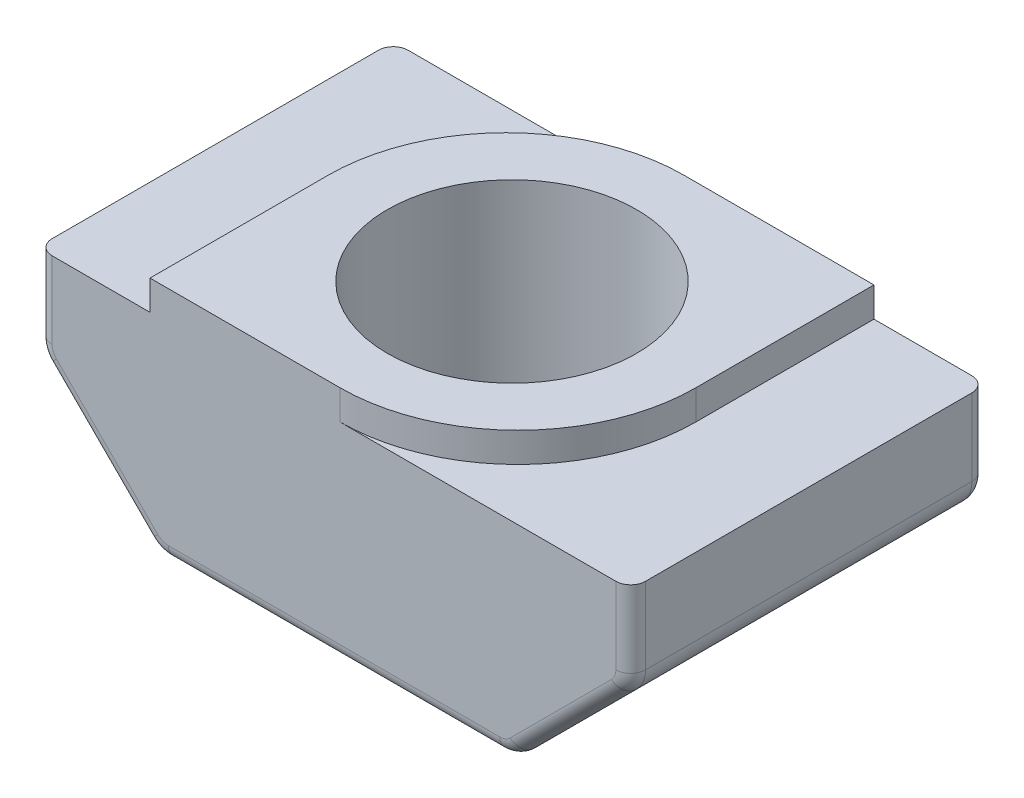
SolidWorks part; units mm, degrees
material "1023 Carbon Steel Sheet (SS)"
ref_plane "Front" through (0, 0, 0) normal (0, 0, 1) x (1, 0, 0)
ref_plane "Top" through (0, 0, 0) normal (0, 1, 0) x (1, 0, 0)
ref_plane "Right" through (0, 0, 0) normal (1, 0, 0) x (0, 0, -1)
sketch "Sketch1" plane through (0, 0, 0) normal (0, 0, 1) x (1, 0, 0)
  line L0 (3.1, 0) -> (-3.1, 0)
  line L1 (-3.1, 0) -> (-3.1, -0.5)
  line L2 (-3.1, -0.5) -> (-5, -0.5)
  line L3 (-5, -0.5) -> (-5, -2)
  line L4 (-5, -2) -> (-3, -4)
  line L5 (-3, -4) -> (3, -4)
  line L6 (0, -4) -> (0, 0) construction
  line L7 (-21.4155, -64.3546) -> (311.9179, -64.3546) construction
  line L8 (5, -2) -> (3, -4)
  line L9 (5, -0.5) -> (5, -2)
  line L10 (3.1, -0.5) -> (5, -0.5)
  line L11 (3.1, 0) -> (3.1, -0.5)
  point P4 (0, 0)
  dimension "D1" = 10
  dimension "D2" = 6.2
  dimension "D3" = 3.5
  dimension "D4" = 0.5
  dimension "D5" = 135
  dimension "D6" = 1.5
extrude "Boss-Extrude1" add sketch "Sketch1" along normal blind 6
sketch "Sketch2" plane through (0, 0, 0) normal (0, 1, 0) x (1, 0, 0)
  line L0 (-3.1, 0) -> (3.1, -6) construction
  circle A0 centre (0, -3) radius 1.5
  dimension "D1" = 3
hole_wizard "M5 Tapped Hole1" positions "Sketch4" profile "Sketch3" tap size "M5" standard "ISO" end condition through all
sketch "Sketch4" plane through (0, 0, 0) normal (0, 1, 0) x (-1, 0, 0)
  point P0 (0, 3)
sketch "Sketch3" plane through (0, 0, 3) normal (1, 0, 0) x (0, 0, 1)
  line L0 (0, 0) -> (0, 4)
  line L1 (0, 4) -> (2.1, 4)
  line L2 (2.1, 4) -> (2.1, 0)
  line L5 (2.1, 0) -> (0, 0)
  line L11 (0, -6.35) -> (0, 107.95) construction
  dimension "Thru Tap Drill Dia." = 4.2
  dimension "Thru Tap Drill Depth" = 4
cosmetic thread "Hole Thread1" parameters "D2"=5
fillet "Fillet1" radius 3 2 edges at (-3.1, -0.25, 0) (3.1, -0.25, 6)
fillet "Fillet2" radius 0.5 4 edges at (5, -2, 3) (3, -4, 3) (-5, -2, 3) (-3, -4, 3)
fillet "Fillet3" radius 0.25 18 edges at (-5, -1.1464, 0) (-4.9619, -1.9842, 0) (-4, -3, 0) (-2.9842, -3.9619, 0) (5, -1.1464, 0) (4.9619, -1.9842, 0) (4, -3, 0) (2.9842, -3.9619, 0) (-5, -1.1464, 6) (-4.9619, -1.9842, 6) (-4, -3, 6) (-2.9842, -3.9619, 6) (5, -1.1464, 6) (4.9619, -1.9842, 6) (4, -3, 6) (2.9842, -3.9619, 6) (0, -4, 0) (0, -4, 6)
